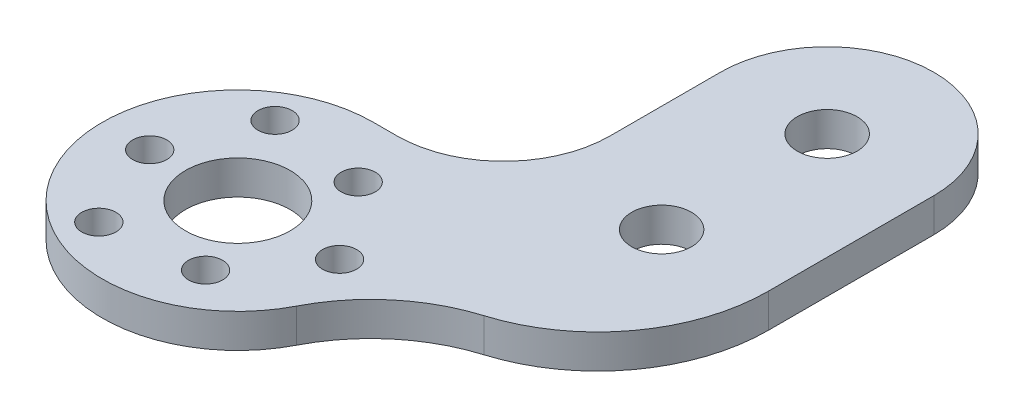
SolidWorks part; units mm, degrees
material "6061-T6 (SS)"
ref_plane "Front Plane" through (0, 0, 0) normal (0, 0, 1) x (1, 0, 0)
ref_plane "Top Plane" through (0, 0, 0) normal (0, 1, 0) x (1, 0, 0)
ref_plane "Right Plane" through (0, 0, 0) normal (1, 0, 0) x (0, 0, -1)
sketch "Sketch1" plane through (0, 0, 0) normal (0, 1, 0) x (1, 0, 0)
  line L66 (12.18, 33) -> (12.18, 22.7)
  line L67 (2.18, 12.7) -> (0, 12.7)
  line L178 (32.18, 33) -> (32.18, 17.5)
  circle A0 centre (22.18, 17.5) radius 2.8
  circle A1 centre (22.18, 33) radius 2.8
  arc A2 (0, 12.7) -> (11.2994, -5.7978) centre (0, 0) ccw
  arc A3 (2.18, 12.7) -> (12.18, 22.7) centre (2.18, 22.7) ccw
  arc A4 (20.8574, 2.199) -> (11.2994, -5.7978) centre (25.5348, -13.1021) ccw
  circle A5 centre (0, 0) radius 4.9
  arc A6 (32.18, 33) -> (12.18, 33) centre (22.18, 33) ccw
  arc A7 (32.18, 17.5) -> (20.8574, 2.199) centre (16.18, 17.5) cw
  circle A8 centre (0, 0) radius 8.25 construction
  circle A9 centre (-8.25, 0) radius 1.6
  circle A10 centre (4.125, 7.1447) radius 1.6
  circle A11 centre (4.125, -7.1447) radius 1.6
  point P15 (0, 0)
  dimension "D1" = 20
  dimension "D2" = 9.8
  dimension "D3" = 25.4
  dimension "D4" = 5.6
  dimension "D5" = 5.6
  dimension "D6" = 15.5
  dimension "D7" = 17.5
  dimension "D8" = 16.5
  dimension "D11" = 10
  dimension "D12" = 22.18
  dimension "D13" = 16
  dimension "D14" = 3.2
  dimension "D9" = 16
  dimension "D15" = 3
extrude "Boss-Extrude1" add sketch "Sketch1" along normal blind 3.175
sketch "Sketch2" plane through (0, 3.175, 0) normal (0, 1, 0) x (1, 0, 0)
  line L0 (22.18, 33) -> (22.18, 17.5) construction
ref_plane "Plane1" through (22.18, 0, 0) normal (-1, 0, 0) x (0, 0, 1)
sketch "Sketch3" plane through (0, 3.175, 0) normal (0, 1, 0) x (1, 0, 0)
  circle A0 centre (0, 0) radius 9.5263 construction
  circle A1 centre (9.5263, 0) radius 1.6
  circle A2 centre (-4.7631, -8.25) radius 1.6
  circle A3 centre (-4.7631, 8.25) radius 1.6
  point P11 (0, 0)
  dimension "D1" = 3
  dimension "D2" = 3.2
  dimension "D3" = 16.5
extrude "Cut-Extrude1" cut sketch "Sketch3" against normal up to next
